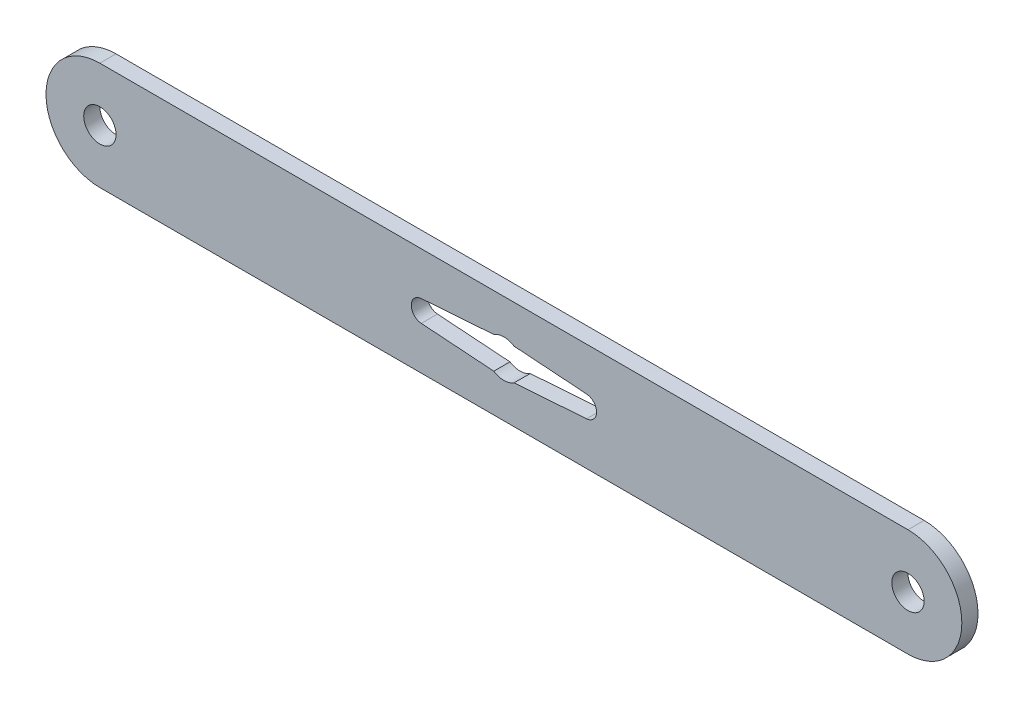
SolidWorks part; units mm, degrees
material "Acrylic (Medium-high impact)"
ref_plane "Front Plane" through (0, 0, 0) normal (0, 0, 1) x (1, 0, 0)
ref_plane "Top Plane" through (0, 0, 0) normal (0, 1, 0) x (1, 0, 0)
ref_plane "Right Plane" through (0, 0, 0) normal (1, 0, 0) x (0, 0, -1)
sketch "Sketch1" plane through (0, 0, 0) normal (0, 0, 1) x (1, 0, 0)
  line L0 (75, 0) -> (-75, 0) construction
  line L1 (75, -10) -> (-75, -10)
  line L2 (75, 10) -> (-75, 10)
  line L3 (-1.8835, 2.95) -> (-15.3416, 1.995)
  line L5 (0, 3.5) -> (0, -3.5) construction
  line L11 (-1.8835, -2.95) -> (-15.3416, -1.995)
  line L12 (1.8835, -2.95) -> (15.3416, -1.995)
  line L13 (1.8835, 2.95) -> (15.3416, 1.995)
  arc A0 (75, -10) -> (75, 10) centre (75, 0) ccw
  arc A1 (-75, 10) -> (-75, -10) centre (-75, 0) ccw
  circle A2 centre (75, 0) radius 3
  circle A3 centre (-75, 0) radius 3
  arc A16 (-1.8835, -2.95) -> (1.8835, -2.95) centre (0, 0) ccw
  arc A17 (-15.3416, 1.995) -> (-15.3416, -1.995) centre (-15.2, 0) ccw
  arc A18 (15.3416, 1.995) -> (15.3416, -1.995) centre (15.2, 0) cw
  arc A19 (-1.8835, 2.95) -> (-3.5, 0) centre (0, 0) ccw construction
  arc A20 (-3.5, 0) -> (-1.8835, -2.95) centre (0, 0) ccw construction
  arc A21 (1.8835, -2.95) -> (3.5, 0) centre (0, 0) ccw construction
  arc A22 (1.8835, 2.95) -> (-1.8835, 2.95) centre (0, 0) ccw
  arc A23 (3.5, 0) -> (1.8835, 2.95) centre (0, 0) ccw construction
  point P2 (0, 0)
  point P25 (-17.2, 0)
  dimension "D2" = 6
  dimension "D8" = 2
  dimension "D4" = 6
  dimension "D6" = 5.9
  dimension "D7" = 17.2
  dimension "D5" = 7
  dimension "D1" = 150
  dimension "D3" = 20
extrude "Boss-Extrude1" add sketch "Sketch1" along normal blind 3
